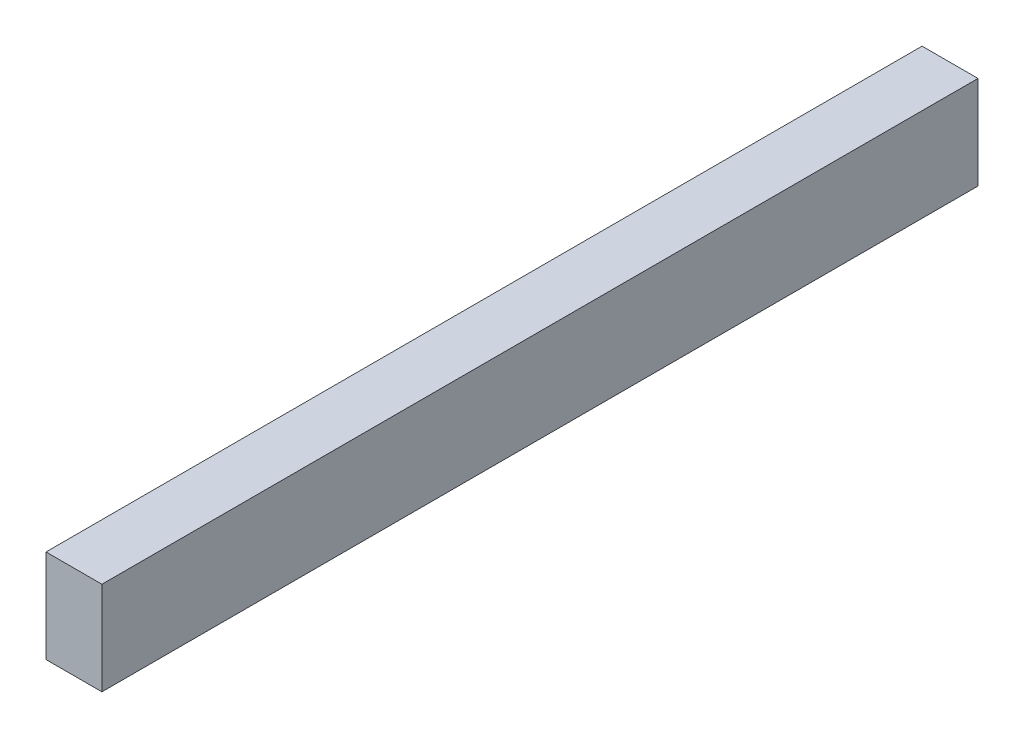
SolidWorks part; units mm, degrees
ref_plane "Front Plane" through (0, 0, 0) normal (0, 0, 1) x (1, 0, 0)
ref_plane "Top Plane" through (0, 0, 0) normal (0, 1, 0) x (1, 0, 0)
ref_plane "Right Plane" through (0, 0, 0) normal (1, 0, 0) x (0, 0, -1)
sketch "Sketch1" plane through (0, 0, 0) normal (0, 0, 1) x (1, 0, 0)
  line L1 (-19.05, -31.75) -> (19.05, -31.75)
  line L2 (-19.05, -31.75) -> (-19.05, 31.75)
  line L3 (-19.05, 31.75) -> (19.05, 31.75)
  line L4 (19.05, -31.75) -> (19.05, 31.75)
  line L5 (-19.05, -31.75) -> (19.05, 31.75) construction
  line L6 (-19.05, 31.75) -> (19.05, -31.75) construction
  point P0 (0, 0)
  dimension "D1" = 38.1
  dimension "D2" = 63.5
extrude "Boss-Extrude1" add sketch "Sketch1" along normal blind 596.9
